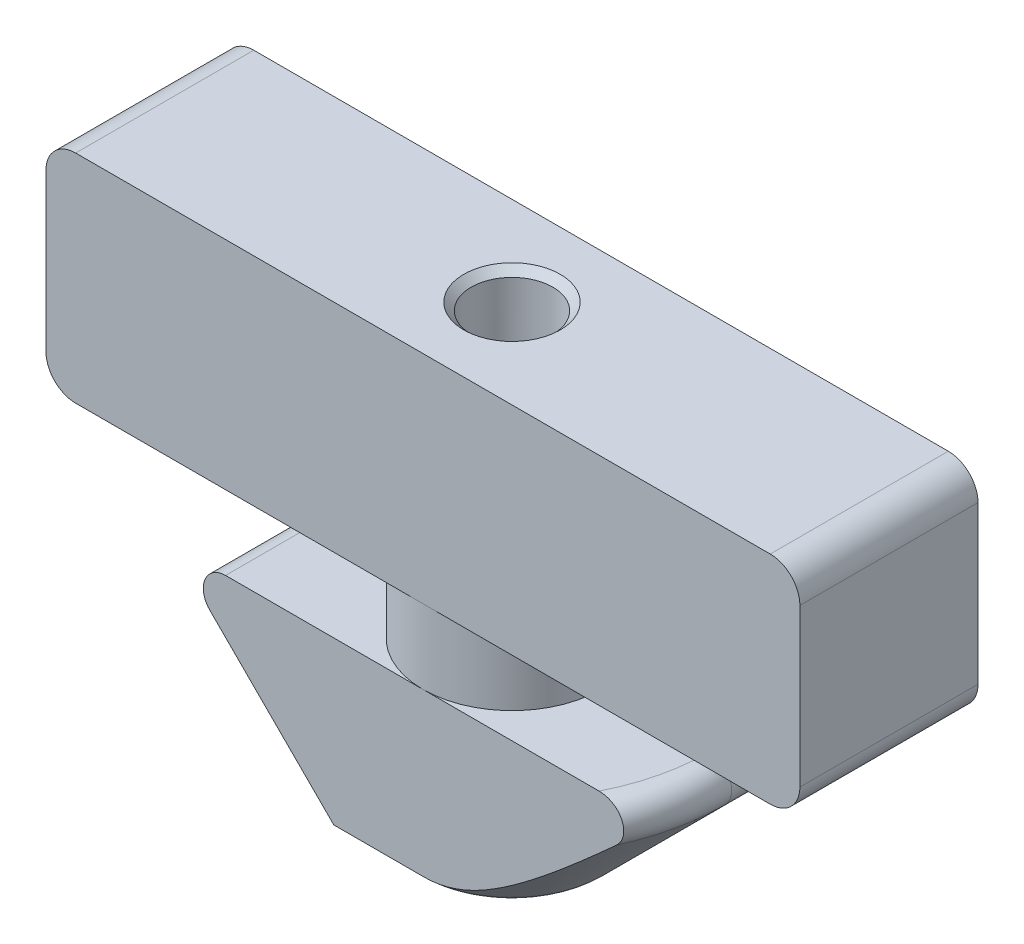
SolidWorks part; units mm, degrees
ref_plane "Front Plane" through (0, 0, 0) normal (0, 0, 1) x (1, 0, 0)
ref_plane "Top Plane" through (0, 0, 0) normal (0, 1, 0) x (1, 0, 0)
ref_plane "Right Plane" through (0, 0, 0) normal (1, 0, 0) x (0, 0, -1)
sketch "Sketch1" plane through (0, 0, 0) normal (0, 0, 1) x (1, 0, 0)
  line L1 (-12.7, 3.65) -> (12.7, 3.65)
  line L2 (-12.7, 3.65) -> (-12.7, -3.65)
  line L3 (-12.7, -3.65) -> (12.7, -3.65)
  line L5 (-12.7, 3.65) -> (12.7, -3.65) construction
  line L6 (-12.7, -3.65) -> (12.7, 3.65) construction
  line L11 (12.7, 3.65) -> (12.7, -3.65)
  point P0 (0, 0)
  point P6 (0, 0)
  dimension "D3" = 7.3
  dimension "D4" = 25.4
extrude "Boss-Extrude1" add sketch "Sketch1" along normal blind 6
ref_plane "Plane1" through (0, 0, 3) normal (0, 0, 1) x (1, 0, 0)
sketch "Sketch2" plane through (0, 0, 3) normal (0, 0, 1) x (1, 0, 0)
  line L0 (0, 0) -> (0, -11.85) construction
  line L4 (6.65, -6.15) -> (3, -6.15)
  line L5 (3, -6.15) -> (3, -3.65)
  line L6 (-12.7, -3.65) -> (12.7, -3.65) construction
  line L7 (3, -3.65) -> (0, -3.65)
  line L8 (0, -3.65) -> (0, -11.85)
  line L15 (3.3, -3.9) -> (3.3, -5.9) construction
  line L16 (3.3, -5.9) -> (7.65, -5.9) construction
  line L17 (0, -11.85) -> (2.3464, -11.85)
  line L18 (7.3571, -7.6071) -> (2.8642, -12.1) construction
  line L19 (2.8642, -12.1) -> (0, -12.1) construction
  line L20 (7.1803, -7.4303) -> (3.0536, -11.5571)
  line L21 (7.65, -6.9) -> (7.65, -5.9) construction
  arc A0 (6.65, -5.9) -> (7.3571, -7.6071) centre (6.65, -6.9) cw construction
  arc A1 (6.65, -6.15) -> (7.1803, -7.4303) centre (6.65, -6.9) cw
  arc A2 (2.3464, -11.85) -> (3.0536, -11.5571) centre (2.3464, -10.85) ccw
  dimension "D12" = 1
  dimension "D10" = 0.75
  dimension "D2" = 1
  dimension "D1" = 2.5
  dimension "D3" = 2
  dimension "D4" = 8.2
  dimension "D5" = 3
  dimension "D6" = 0.25
  dimension "D7" = 7.65
  dimension "D8" = 3.3
  dimension "D9" = 135
  dimension "D11" = 0.25
  dimension "D13" = 0.25
revolve "Revolve1" add sketch "Sketch2" angle 360 about L0
sketch "Sketch3" plane through (0, 0, 0) normal (1, 0, 0) x (0, 0, -1)
  line L27 (-5.3464, -11.85) -> (-0.6536, -11.85) construction
  line L28 (-6, -6.15) -> (-10.4, -6.15)
  line L29 (-6, -6.15) -> (-6, -11.85)
  line L30 (-6, -11.85) -> (-10.4, -11.85)
  line L31 (-10.4, -6.15) -> (-10.4, -11.85)
  line L32 (-3, 0) -> (-3, -11.85) construction
  line L34 (4.4, -6.15) -> (4.4, -11.85)
  line L35 (0, -11.85) -> (4.4, -11.85)
  line L36 (0, -6.15) -> (0, -11.85)
  line L37 (0, -6.15) -> (4.4, -6.15)
  arc A0 (-9.65, -6.15) -> (-10.1803, -7.4303) centre (-9.65, -6.9) ccw construction
  point P4 (-3, 6.35)
  point P9 (0, 0)
extrude "Cut-Extrude1" cut sketch "Sketch3" against normal through all both and the other way through all
sketch "Sketch5" plane through (0, 0, 0) normal (0, 0, -1) x (-1, 0, 0)
  line L10 (-7.1803, -7.4303) -> (-3.0536, -11.5571)
  line L11 (-6.65, -6.15) -> (0, -6.15)
  line L12 (0, -6.15) -> (0, -11.85)
  line L13 (-2.3464, -11.85) -> (2.3464, -11.85) construction
  line L14 (0, -11.85) -> (-2.3464, -11.85)
  arc A0 (-7.1803, -7.4303) -> (-6.65, -6.15) centre (-6.65, -6.9) cw
  arc A1 (-2.3464, -11.85) -> (-3.0536, -11.5571) centre (-2.3464, -10.85) cw
extrude "Boss-Extrude3" add sketch "Sketch5" against normal up to next
sketch "Sketch6" plane through (0, 0, 6) normal (0, 0, 1) x (1, 0, 0)
  line L12 (0, -6.15) -> (0, -11.85)
  line L13 (0, -11.85) -> (-2.3464, -11.85)
  line L14 (-7.1803, -7.4303) -> (-3.0536, -11.5571)
  line L15 (-6.65, -6.15) -> (0, -6.15)
  arc A0 (-3.0536, -11.5571) -> (-2.3464, -11.85) centre (-2.3464, -10.85) ccw
  arc A1 (-7.1803, -7.4303) -> (-6.65, -6.15) centre (-6.65, -6.9) cw
extrude "Boss-Extrude4" add sketch "Sketch6" against normal up to next
fillet "Fillet1" radius 1 4 edges at (-12.7, -3.65, 3) (-12.7, 3.65, 3) (12.7, -3.65, 3) (12.7, 3.65, 3)
sketch "Sketch7" plane through (0, 0, 0) normal (-1, 0, 0) x (0, 0, 1)
  line L0 (0, -11.6069) -> (0, -11.85)
  line L1 (0, -11.85) -> (0.6536, -11.85)
  arc A0 (0, -11.6069) -> (0.6536, -11.85) centre (0.6536, -10.85) ccw
extrude "Cut-Extrude2" cut sketch "Sketch7" against normal through all
sketch "Sketch8" plane through (0, 0, 0) normal (1, 0, 0) x (0, 0, -1)
  line L0 (-6, -11.6069) -> (-6, -11.85)
  line L1 (-6, -11.85) -> (-5.3464, -11.85)
  arc A0 (-5.3464, -11.85) -> (-6, -11.6069) centre (-5.3464, -10.85) cw
extrude "Cut-Extrude3" cut sketch "Sketch8" against normal through all
sketch "Sketch9" plane through (0, 3.65, 0) normal (0, 1, 0) x (1, 0, 0)
  line L0 (-11.7, 0) -> (-11.7, -6) construction
  circle A0 centre (0, -3) radius 1.375
  point P2 (-11.7, -3)
  dimension "D1" = 2.75
extrude "Cut-Extrude4" cut sketch "Sketch9" against normal blind 8
chamfer "Chamfer1" distance 0.25 angle 45 1 edges at (0, 3.65, 4.375)
